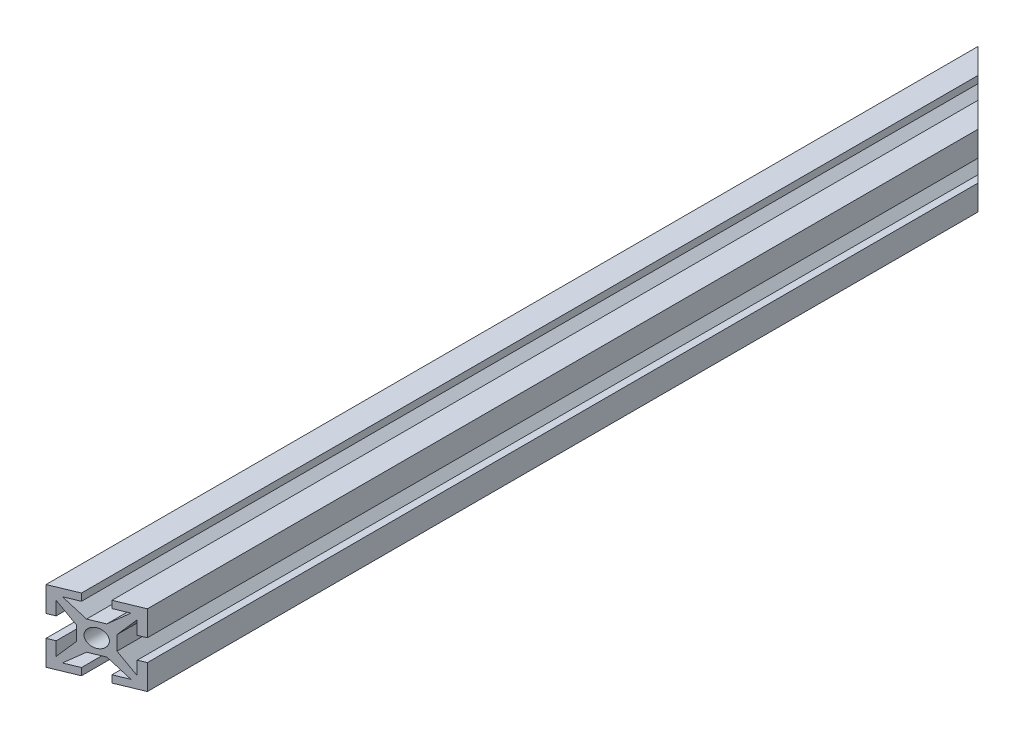
SolidWorks part; units mm, degrees
ref_plane "Front Plane" through (0, 0, 0) normal (0, 0, 1) x (1, 0, 0)
ref_plane "Top Plane" through (0, 0, 0) normal (0, 1, 0) x (1, 0, 0)
ref_plane "Right Plane" through (0, 0, 0) normal (1, 0, 0) x (0, 0, -1)
sketch "Esquisse2" plane through (0, 0, 0) normal (0, 0, 1) x (1, 0, 0)
  line L0 (-1, -2) -> (1, -2)
  line L1 (1, -2) -> (3.3835, -4)
  line L2 (3.3835, -4) -> (1.5, -4)
  line L3 (1.5, -4) -> (1.5, -5)
  line L4 (1.5, -5) -> (5, -5)
  line L5 (-1, -2) -> (-3.3835, -4)
  line L6 (-3.3835, -4) -> (-1.5, -4)
  line L7 (-1.5, -4) -> (-1.5, -5)
  line L8 (-1.5, -5) -> (-5, -5)
  line L9 (-5, -5) -> (-5, -1.5)
  line L10 (-5, -1.5) -> (-4, -1.5)
  line L11 (-4, -1.5) -> (-4, -3.3835)
  line L12 (-4, -3.3835) -> (-2, -1)
  line L13 (-2, -1) -> (-2, 1)
  line L14 (-2, 1) -> (-4, 3.3835)
  line L15 (-4, 3.3835) -> (-4, 1.5)
  line L16 (-4, 1.5) -> (-5, 1.5)
  line L17 (-5, 1.5) -> (-5, 5)
  line L18 (-5, 5) -> (-1.5, 5)
  line L19 (-1.5, 5) -> (-1.5, 4)
  line L20 (-1.5, 4) -> (-3.3835, 4)
  line L21 (-3.3835, 4) -> (-1, 2)
  line L22 (-1, 2) -> (1, 2)
  line L23 (1, 2) -> (3.3835, 4)
  line L24 (3.3835, 4) -> (1.5, 4)
  line L25 (1.5, 4) -> (1.5, 5)
  line L26 (1.5, 5) -> (5, 5)
  line L27 (5, 5) -> (5, 1.5)
  line L28 (5, 1.5) -> (4, 1.5)
  line L29 (4, 1.5) -> (4, 3.3835)
  line L30 (4, 3.3835) -> (2, 1)
  line L31 (2, -1) -> (2, 1)
  line L32 (2, -1) -> (4, -3.3835)
  line L33 (4, -3.3835) -> (4, -1.5)
  line L34 (4, -1.5) -> (5, -1.5)
  line L35 (5, -1.5) -> (5, -5)
  circle A0 centre (0, 0) radius 1.25
  point P4 (0, -2)
  point P34 (0, 2)
  point P40 (2, 0)
  dimension "D4" = 2.5
  dimension "D1" = 2
  dimension "D2" = 3.5
  dimension "D3" = 1
  dimension "D5" = 10
  dimension "D6" = 10
  dimension "D7" = 140
  dimension "D8" = 4
  dimension "D9" = 4
  dimension "D10" = 3.5
  dimension "D11" = 3
extrude "Boss.-Extru.1" add sketch "Esquisse2" along normal blind 130
sketch "Esquisse3" plane through (0, 5, 0) normal (0, 1, 0) x (1, 0, 0)
  line L0 (-5, 0) -> (5, 0)
  line L1 (-1.5, 0) -> (-5, 0) construction
  line L2 (5, 0) -> (5, -10)
  line L3 (5, -130) -> (5, 0) construction
  line L4 (5, -10) -> (-5, 0)
  line L5 (-5, -130) -> (-5, 0) construction
  line L6 (5, -125.8579) -> (-5, -130)
  line L7 (-5, -130) -> (5, -130)
  line L8 (5, -130) -> (5, -125.8579)
  dimension "D1" = 45
  dimension "D2" = 22.5
extrude "Enlèv. mat.-Extru.1" cut sketch "Esquisse3" against normal through all
